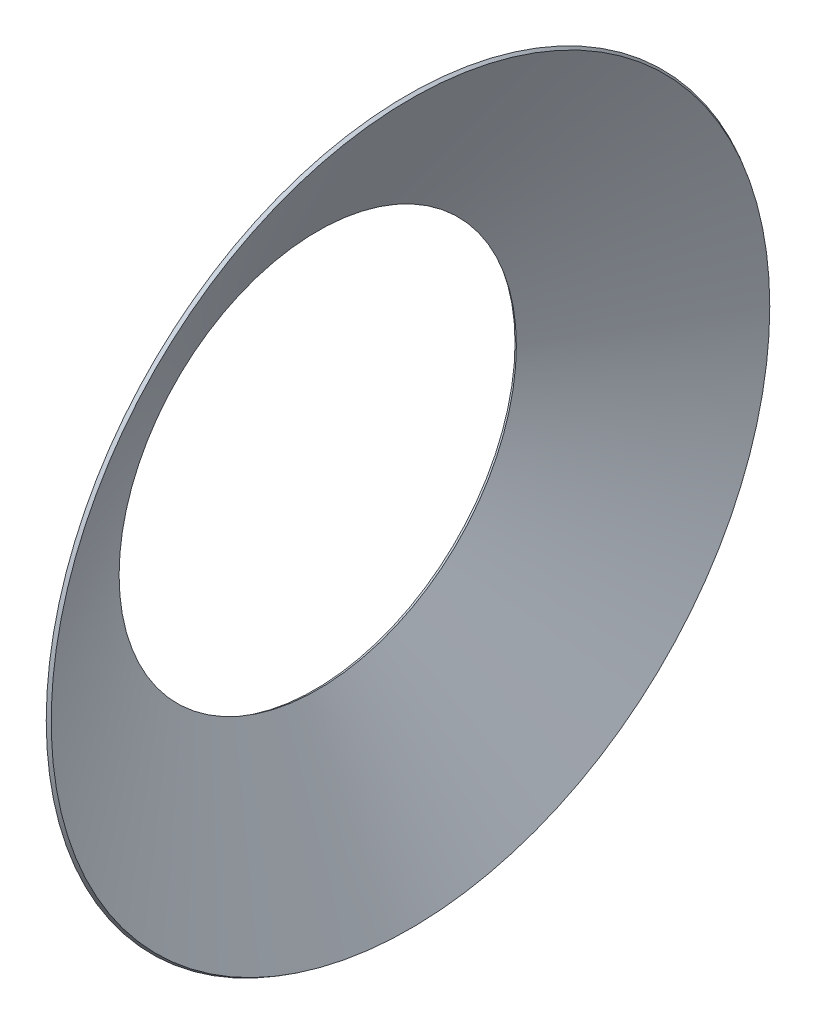
SolidWorks part; units mm, degrees
ref_plane "Plano frontal" through (0, 0, 0) normal (0, 0, 1) x (1, 0, 0)
ref_plane "Plano superior" through (0, 0, 0) normal (0, 1, 0) x (1, 0, 0)
ref_plane "Plano direito" through (0, 0, 0) normal (1, 0, 0) x (0, 0, -1)
sketch "Esboço1" plane through (0, 0, 0) normal (0, 0, 1) x (1, 0, 0)
  line L0 (0, 0) -> (-5587, 0) construction
  line L1 (-5587, 0) -> (-2705, 4992) construction
  line L2 (-2751.65, 4961.1978) -> (-2708.3483, 4936.1987)
  line L3 (-2751.65, 4961.1978) -> (-4025.9182, 2753.9991)
  line L4 (-4025.9182, 2753.9991) -> (-3982.6164, 2729)
  line L5 (-3982.6164, 2729) -> (-2708.3483, 4936.1987)
  point P6 (-2729.9991, 4948.6982)
  dimension "D1" = 5587
  dimension "D2" = 2705
  dimension "D3" = 4992
  dimension "D4" = 50
  dimension "D5" = 50
  dimension "D6" = 2729
revolve "Revolução1" add sketch "Esboço1" angle 360 about L0
